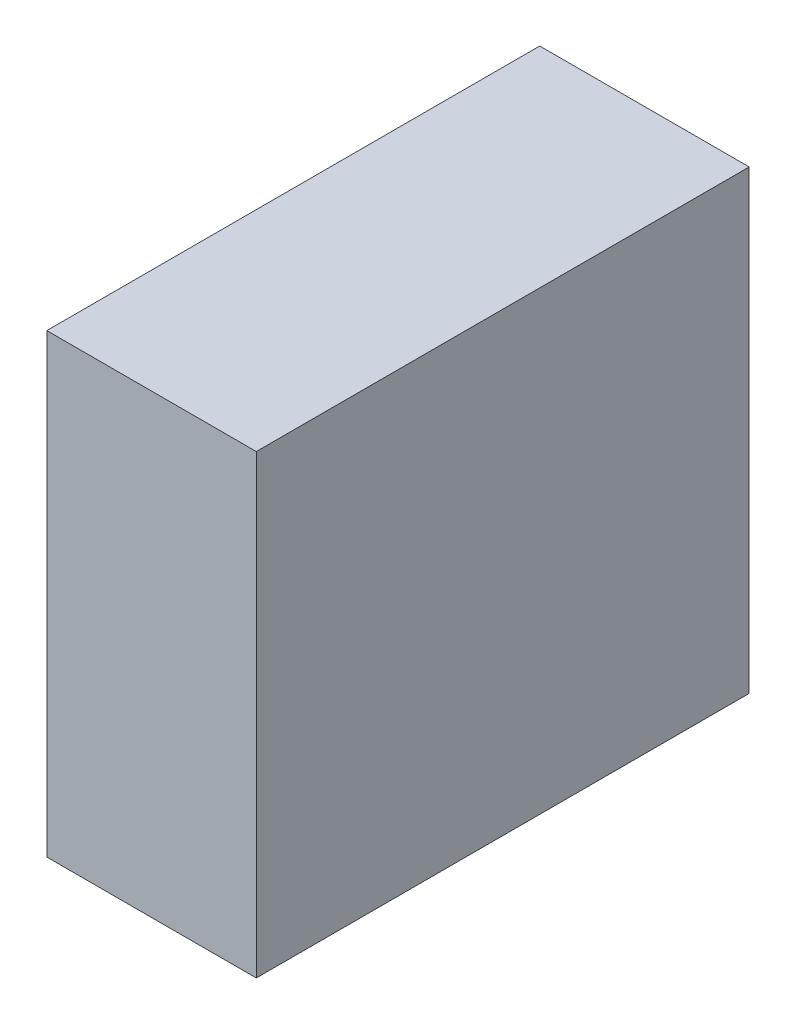
SolidWorks part; units mm, degrees
ref_plane "Front Plane" through (0, 0, 0) normal (0, 0, 1) x (1, 0, 0)
ref_plane "Top Plane" through (0, 0, 0) normal (0, 1, 0) x (1, 0, 0)
ref_plane "Right Plane" through (0, 0, 0) normal (1, 0, 0) x (0, 0, -1)
sketch "Sketch1" plane through (0, 0, 0) normal (0, 0, 1) x (1, 0, 0)
  line L1 (0, 0) -> (170, 0)
  line L2 (0, 0) -> (0, 370)
  line L3 (0, 370) -> (170, 370)
  line L4 (170, 0) -> (170, 370)
  dimension "D1" = 170
  dimension "D2" = 370
extrude "Extrude1" add sketch "Sketch1" along normal blind 400
